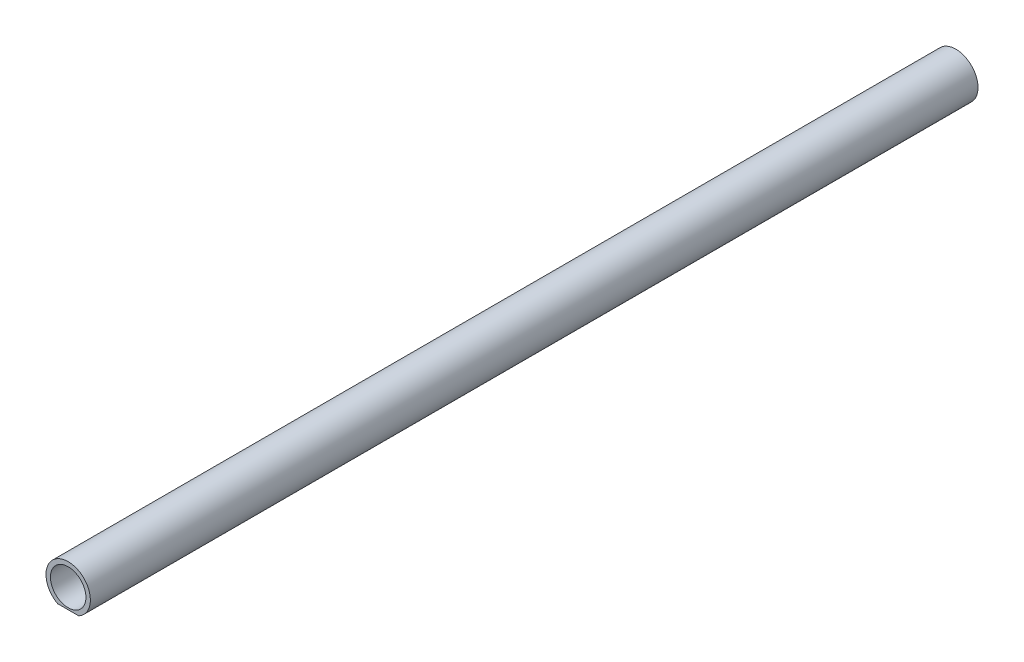
SolidWorks part; units mm, degrees
ref_plane "Front Plane" through (0, 0, 0) normal (0, 0, 1) x (1, 0, 0)
ref_plane "Top Plane" through (0, 0, 0) normal (0, 1, 0) x (1, 0, 0)
ref_plane "Right Plane" through (0, 0, 0) normal (1, 0, 0) x (0, 0, -1)
sketch "Sketch1" plane through (0, 0, 0) normal (0, 0, 1) x (1, 0, 0)
  line L0 (-11.8743, -15.6619) -> (11.8743, -15.6619)
  circle A0 centre (0, 6.3381) radius 20
  arc A1 (11.8743, -15.6619) -> (-11.8743, -15.6619) centre (0, 6.3381) ccw
  dimension "D1" = 50
  dimension "D2" = 40
  dimension "D3" = 22
extrude "Boss-Extrude1" add sketch "Sketch1" along normal blind 1000
